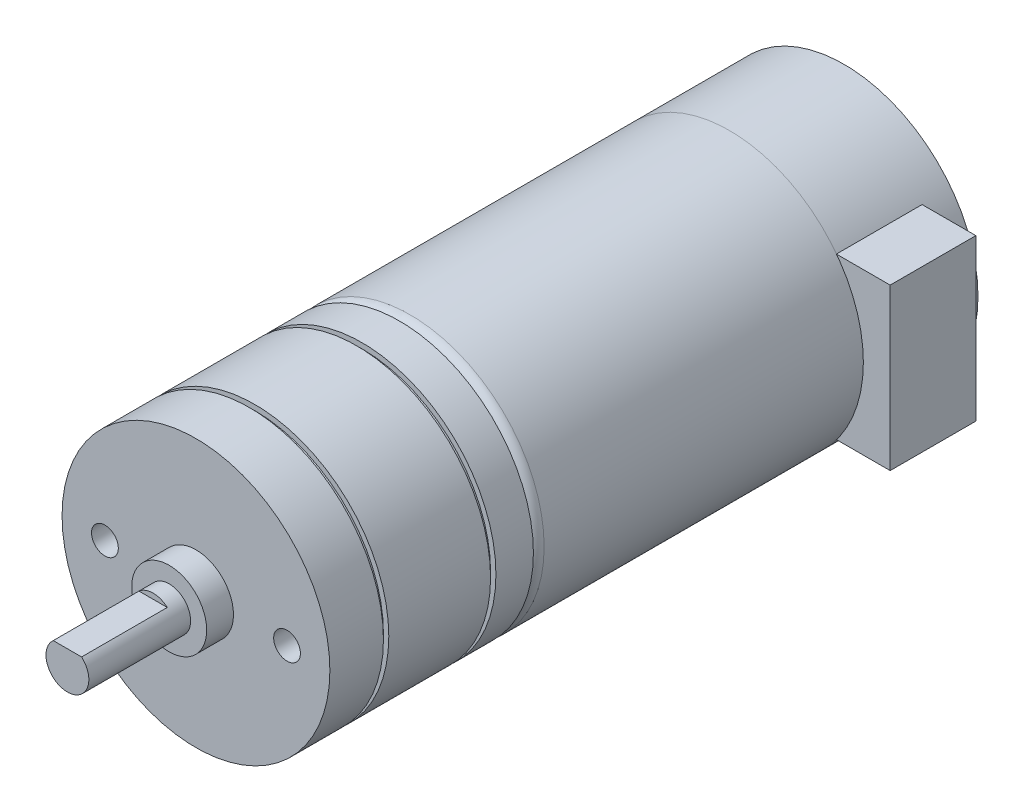
SolidWorks part; units mm, degrees
material "5052-O"
ref_plane "前基準面" through (0, 0, 0) normal (0, 0, 1) x (1, 0, 0)
ref_plane "上基準面" through (0, 0, 0) normal (0, 1, 0) x (1, 0, 0)
ref_plane "右基準面" through (0, 0, 0) normal (1, 0, 0) x (0, 0, -1)
sketch "草圖1" plane through (0, 0, 0) normal (0, 0, 1) x (1, 0, 0)
  circle A0 centre (0, 0) radius 12.5
  dimension "D1" = 25
extrude "填料-伸長1" add sketch "草圖1" along normal blind 30.8
sketch "草圖2" plane through (0, 0, 0) normal (0, 0, -1) x (-1, 0, 0)
  circle A1 centre (0, 0) radius 12.5
  circle A2 centre (0, 0) radius 12.5
  dimension "D1" = 0
extrude "填料-伸長2" add sketch "草圖2" along normal blind 10.7 separate body
sketch "草圖3" plane through (0, 0, 0) normal (1, 0, 0) x (0, 0, -1)
  line L0 (0, -12.5) -> (0, 12.5) construction
  line L1 (0, -7.5) -> (8, -7.5)
  line L2 (0, -7.5) -> (0, 7.5)
  line L3 (0, 7.5) -> (8, 7.5)
  line L4 (8, -7.5) -> (8, 7.5)
  dimension "D1" = 15
  dimension "D2" = 8
extrude "填料-伸長3" add sketch "草圖3" along normal blind 15 separate body
fillet "圓角1" radius 1 1 edges at (12.5, 0, 30.8)
sketch "草圖4" plane through (0, 0, 30.8) normal (0, 0, 1) x (1, 0, 0)
  circle A0 centre (0, 0) radius 12.5
  dimension "D1" = 25
extrude "填料-伸長4" add sketch "草圖4" along normal blind 19 separate body
sketch "草圖5" plane through (0, 0, 49.8) normal (0, 0, 1) x (1, 0, 0)
  circle A0 centre (0, 0) radius 12.5
  circle A1 centre (0, 0) radius 12
  dimension "D1" = 24
  dimension "D2" = 25
extrude "除料-伸長1" cut sketch "草圖5" against normal blind 0.5 from offset 15 offset against normal yes
pattern_linear "直線複製排列1" count 2 spacing 10 along (0, 0, 1) of "除料-伸長1"
sketch "草圖6" plane through (0, 0, 49.8) normal (0, 0, 1) x (1, 0, 0)
  circle A0 centre (0, 0) radius 3.5
  dimension "D1" = 7
extrude "填料-伸長5" add sketch "草圖6" along normal blind 2.5 separate body
sketch "草圖7" plane through (0, 0, 52.3) normal (0, 0, 1) x (1, 0, 0)
  circle A0 centre (0, 0) radius 2
  dimension "D1" = 4
extrude "填料-伸長6" add sketch "草圖7" along normal blind 9.5
sketch "草圖8" plane through (0, 0, 61.8) normal (0, 0, 1) x (1, 0, 0)
  line L0 (-1.3229, 1.5) -> (1.3229, 1.5)
  circle A0 centre (0, 0) radius 2 construction
  arc A1 (-1.3229, 1.5) -> (1.3229, 1.5) centre (0, 0) cw
  circle M2 centre (0, 0) radius 2
  dimension "D1" = 1.5
extrude "除料-伸長2" cut sketch "草圖8" against normal blind 8 contours L0 M2
hole_wizard "M3x0.5 螺紋孔1" positions "草圖10" profile "草圖12" tap size "M3x0.5" standard "Ansi Metric"
sketch "草圖10" plane through (0, 0, 49.8) normal (0, 0, 1) x (1, 0, 0)
  circle A0 centre (0, 0) radius 8.5 construction
  point P3 (-8.5, 0)
  point P5 (8.5, 0)
  dimension "D1" = 17
sketch "草圖12" plane through (8.5, 0, 49.8) normal (1, 0, 0) x (0, -1, 0)
  line L0 (0, 0) -> (0, 5.7511)
  line L1 (0, 5.7511) -> (1.25, 5)
  line L2 (1.25, 5) -> (1.25, 0)
  line L5 (1.25, 0) -> (0, 0)
  line L10 (0, 5.7511) -> (-1.25, 5) construction
  line L11 (0, -6.35) -> (0, 107.95) construction
  dimension "螺孔鑽直徑" = 2.5
  dimension "螺孔鑽深度" = 5
  dimension "導頭角度" = 118
